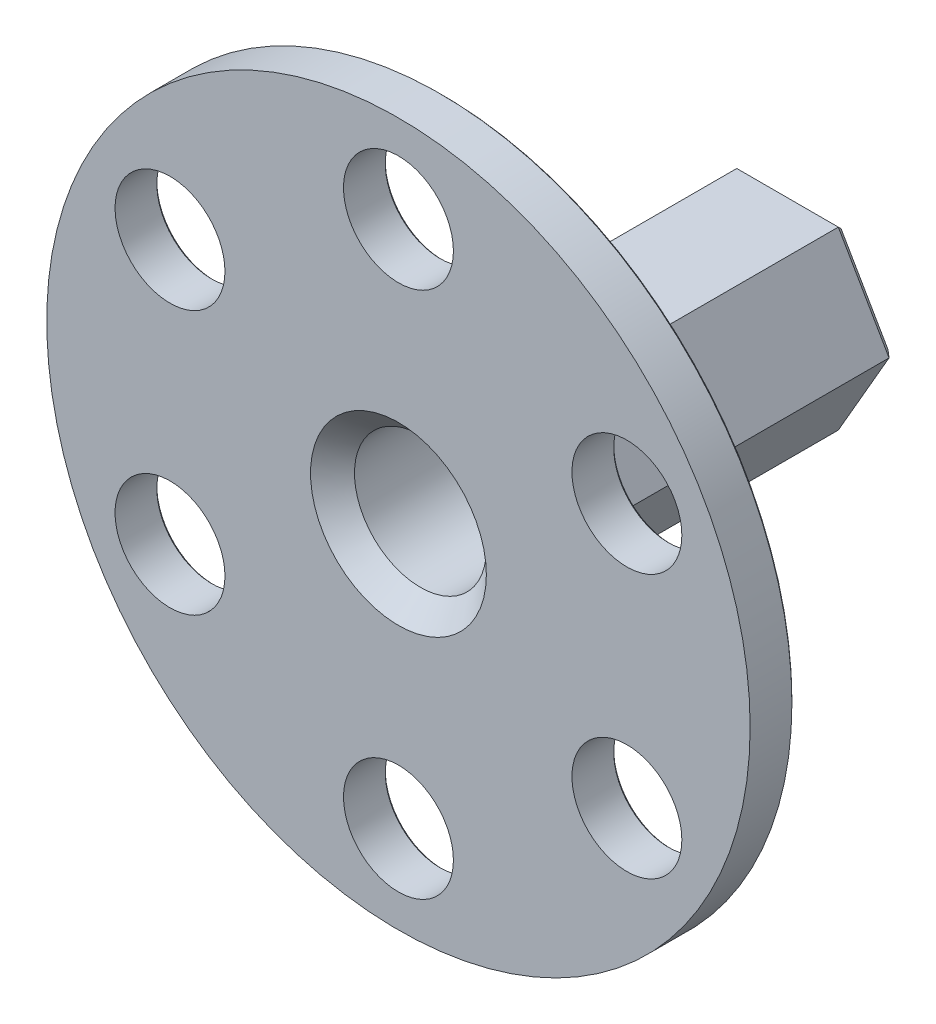
SolidWorks part; units mm, degrees
ref_plane "Front Plane" through (0, 0, 0) normal (0, 0, 1) x (1, 0, 0)
ref_plane "Top Plane" through (0, 0, 0) normal (0, 1, 0) x (1, 0, 0)
ref_plane "Right Plane" through (0, 0, 0) normal (1, 0, 0) x (0, 0, -1)
sketch "Sketch1" plane through (0, 0, 0) normal (0, 0, 1) x (1, 0, 0)
  circle A0 centre (0, 0) radius 32
  dimension "D1" = 64
extrude "Boss-Extrude1" add sketch "Sketch1" against normal blind 4
sketch "Sketch2" plane through (0, 0, 0) normal (0, 0, 1) x (1, 0, 0)
  circle A0 centre (0, 0) radius 24 construction
  circle A1 centre (0, 24) radius 5
  dimension "D1" = 10
  dimension "D2" = 48
extrude "Cut-Extrude1" cut sketch "Sketch2" against normal through all
pattern_circular "CirPattern1" count 6 over 360 about axis through (0, 0, 0) along (0, 0, 1) of "Cut-Extrude1"
sketch "Sketch3" plane through (0, 0, -4) normal (0, 0, -1) x (-1, 0, 0)
  line L1 (-4.6188, 8) -> (-9.2376, 0)
  line L2 (-9.2376, 0) -> (-4.6188, -8)
  line L3 (-4.6188, -8) -> (4.6188, -8)
  line L4 (4.6188, -8) -> (9.2376, 0)
  line L5 (9.2376, 0) -> (4.6188, 8)
  line L6 (4.6188, 8) -> (-4.6188, 8)
  circle A0 centre (0, 0) radius 8 construction
  dimension "D1" = 16
extrude "Boss-Extrude2" add sketch "Sketch3" along normal blind 32
chamfer "Chamfer1" distance 2 angle 45 6 edges at (6.9282, 4, -4) (6.9282, -4, -4) (0, -8, -4) (-6.9282, -4, -4) (-6.9282, 4, -4) (0, 8, -4)
chamfer "Chamfer2" distance 0.2 angle 45 7 edges at (-5, -24, -4) (18.2846, -16.3301, -4) (23.2846, 7.6699, -4) (5, 24, -4) (-18.2846, 16.3301, -4) (-23.2846, -7.6699, -4) (32, 0, -4)
sketch "Sketch4" plane through (0, 0, 0) normal (0, 0, 1) x (1, 0, 0)
  circle A0 centre (0, 0) radius 6
  dimension "D1" = 12
extrude "Cut-Extrude2" cut sketch "Sketch4" against normal blind 32
chamfer "Chamfer3" distance 0.6 angle 45 6 edges at (-6.9282, 4, -36) (-6.9282, -4, -36) (0, -8, -36) (6.9282, -4, -36) (6.9282, 4, -36) (0, 8, -36)
chamfer "Chamfer4" distance 5 angle 45 1 edges at (6, 0, -32)
chamfer "Chamfer5" distance 2 angle 45 1 edges at (6, 0, 0)
